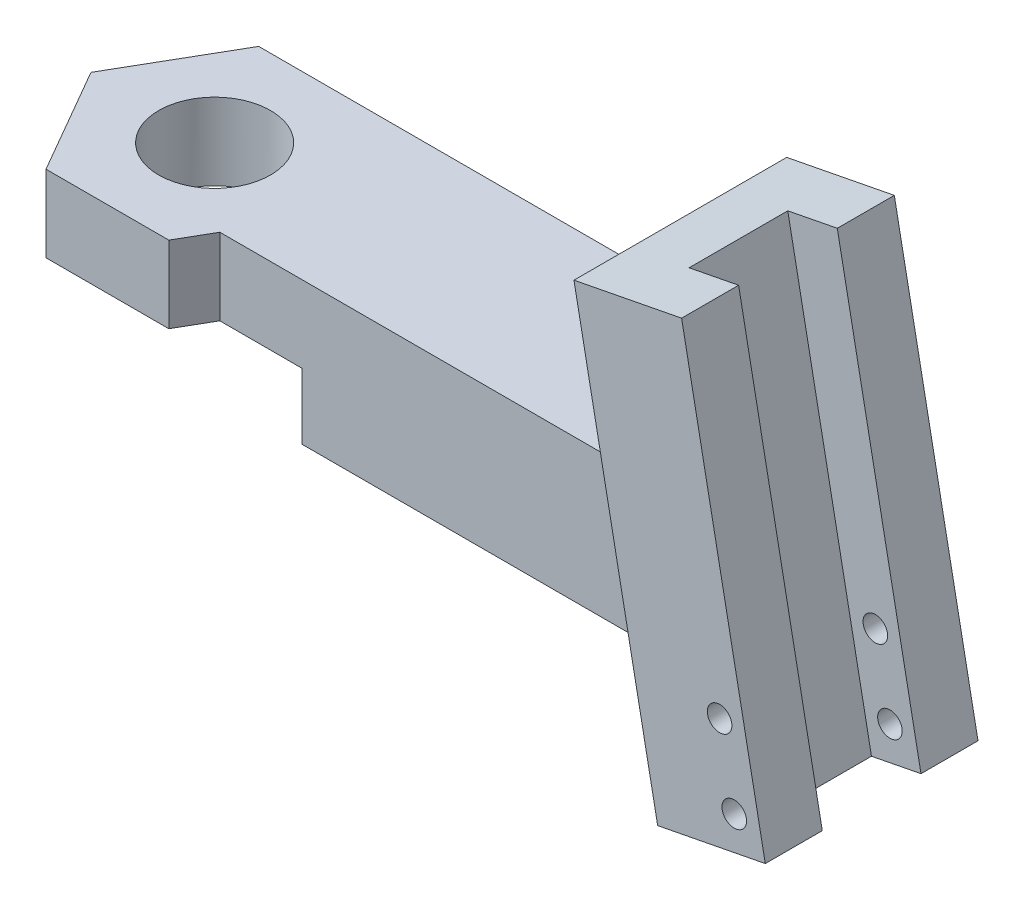
SolidWorks part; units mm, degrees
ref_plane "Front Plane" through (0, 0, 0) normal (0, 0, 1) x (1, 0, 0)
ref_plane "Top Plane" through (0, 0, 0) normal (0, 1, 0) x (1, 0, 0)
ref_plane "Right Plane" through (0, 0, 0) normal (1, 0, 0) x (0, 0, -1)
sketch "Sketch1" plane through (0, 0, 0) normal (0, 1, 0) x (1, 0, 0)
  line L1 (0, 0) -> (25, 0)
  line L2 (0, 0) -> (0, -6.75)
  line L3 (0, -6.75) -> (25, -6.75)
  line L4 (25, 0) -> (25, -6.75)
  dimension "D1" = 6.75
  dimension "D2" = 25
extrude "Boss-Extrude1" add sketch "Sketch1" along normal blind 6.5
ref_plane "Plane1" through (0, 0, 3.375) normal (0, 0, 1) x (1, 0, 0)
sketch "Sketch5" plane through (0, 6.5, 0) normal (0, 1, 0) x (1, 0, 0)
  line L0 (0, 0) -> (0, -6.75) construction
  line L1 (-5.6003, -3.375) -> (-2.8001, -8.225)
  line L2 (-2.8001, -8.225) -> (2.8001, -8.225)
  line L3 (2.8001, -8.225) -> (5.6003, -3.375)
  line L4 (5.6003, -3.375) -> (2.8001, 1.475)
  line L5 (2.8001, 1.475) -> (-2.8001, 1.475)
  line L6 (-2.8001, 1.475) -> (-5.6003, -3.375)
  circle A0 centre (0, -3.375) radius 4.85 construction
  dimension "D1" = 4.85
extrude "Boss-Extrude4" add sketch "Sketch5" against normal up to surface (6.5 mm away) up to face at (12.5, 0, 3.375)
sketch "Sketch3" plane through (0, 0, 3.375) normal (0, 0, 1) x (1, 0, 0)
  line L0 (21.2757, 14.1555) -> (26.1838, 15.1096)
  line L1 (26.1838, 15.1096) -> (30, -4.523)
  line L2 (30, -4.523) -> (25.0919, -5.477)
  line L3 (25.0919, -5.477) -> (21.2757, 14.1555)
  line L4 (3.6517, 6.5) -> (25, 6.5) construction
  point P6 (27.5459, -5)
  dimension "D1" = 30
  dimension "D2" = 5
  dimension "D3" = 20
  dimension "D4" = 79
  dimension "D6" = 5
extrude "Boss-Extrude3" add sketch "Sketch3" against normal up to surface and the other way up to surface up to face at (0, 3.25, -1.475) other way up to face at (0, 3.25, 8.225)
sketch "Sketch4" plane through (-1.8768, 9.6551, 0) normal (-0.1908, 0.9816, 0) x (0.9816, 0.1908, 0)
  line L0 (28.5858, -8.225) -> (28.5858, 1.475) construction
  line L1 (26.2858, -1.125) -> (28.5858, -1.125)
  line L2 (26.2858, -1.125) -> (26.2858, -5.625)
  line L3 (26.2858, -5.625) -> (28.5858, -5.625)
  line L4 (28.5858, -1.125) -> (28.5858, -5.625)
  point P6 (28.5858, -3.375)
  dimension "D1" = 4.5
  dimension "D2" = 2.3
extrude "Cut-Extrude1" cut sketch "Sketch4" against normal blind 23 contours L2 L3 L4 L1
sketch "Sketch6" plane through (0, 6.5, 0) normal (0, 1, 0) x (1, 0, 0)
  circle A0 centre (0, -3.3356) radius 2.55
  dimension "D1" = 5.1
extrude "Cut-Extrude2" cut sketch "Sketch6" against normal blind 10
sketch "Sketch7" plane through (0, 0, -1.475) normal (0, 0, -1) x (-1, 0, 0)
  line L0 (-2.8001, 0) -> (-24.0272, 0)
  line L1 (-24.0272, 0) -> (-25.0919, -5.477)
  line L2 (-25.0919, -5.477) -> (-30, -4.523)
  line L3 (-30, -4.523) -> (-26.1838, 15.1096)
  line L4 (-26.1838, 15.1096) -> (-21.2757, 14.1555)
  line L5 (-21.2757, 14.1555) -> (-22.7638, 6.5)
  line L6 (-22.7638, 6.5) -> (-2.8001, 6.5)
  line L7 (-2.8001, 6.5) -> (-2.8001, 0)
  point P4 (0, 0)
  point P17 (0, 0)
  point P18 (0, 0)
  point P19 (0, 0)
  dimension "D1" = 20
extrude "Boss-Extrude5" add sketch "Sketch7" against normal up to surface (1.475 mm away) up to face at (13.5236, 3.25, 0)
sketch "Sketch8" plane through (0, 0, 0) normal (0, -1, 0) x (-1, 0, 0)
  line L1 (-4.6765, -11.475) -> (4.6765, -11.475)
  line L2 (4.6765, -11.475) -> (9.3531, -3.375)
  line L3 (9.3531, -3.375) -> (4.6765, 4.725)
  line L4 (4.6765, 4.725) -> (-4.6765, 4.725)
  line L5 (-4.6765, 4.725) -> (-9.3531, -3.375)
  line L6 (-9.3531, -3.375) -> (-4.6765, -11.475)
  circle A0 centre (0, -3.375) radius 8.1 construction
  dimension "D1" = 16.2
extrude "Cut-Extrude3" cut sketch "Sketch8" against normal blind 3
sketch "Sketch9" plane through (0, 0, -1.475) normal (0, 0, -1) x (-1, 0, 0)
  line L0 (-30, -4.523) -> (-26.1838, 15.1096) construction
  line L1 (-25.0919, -5.477) -> (-30, -4.523) construction
  circle A0 centre (-28.5849, -3.27) radius 0.56
  circle A1 centre (-27.9171, 0.1657) radius 0.56
  dimension "D1" = 1.12
  dimension "D2" = 1.15
  dimension "D5" = 1.12
  dimension "D3" = 1.5
  dimension "D4" = 5
  dimension "D6" = 1.15
extrude "Cut-Extrude4" cut sketch "Sketch9" against normal up to surface (9.7 mm away) up to face at (25.6378, 4.8163, 8.225)
